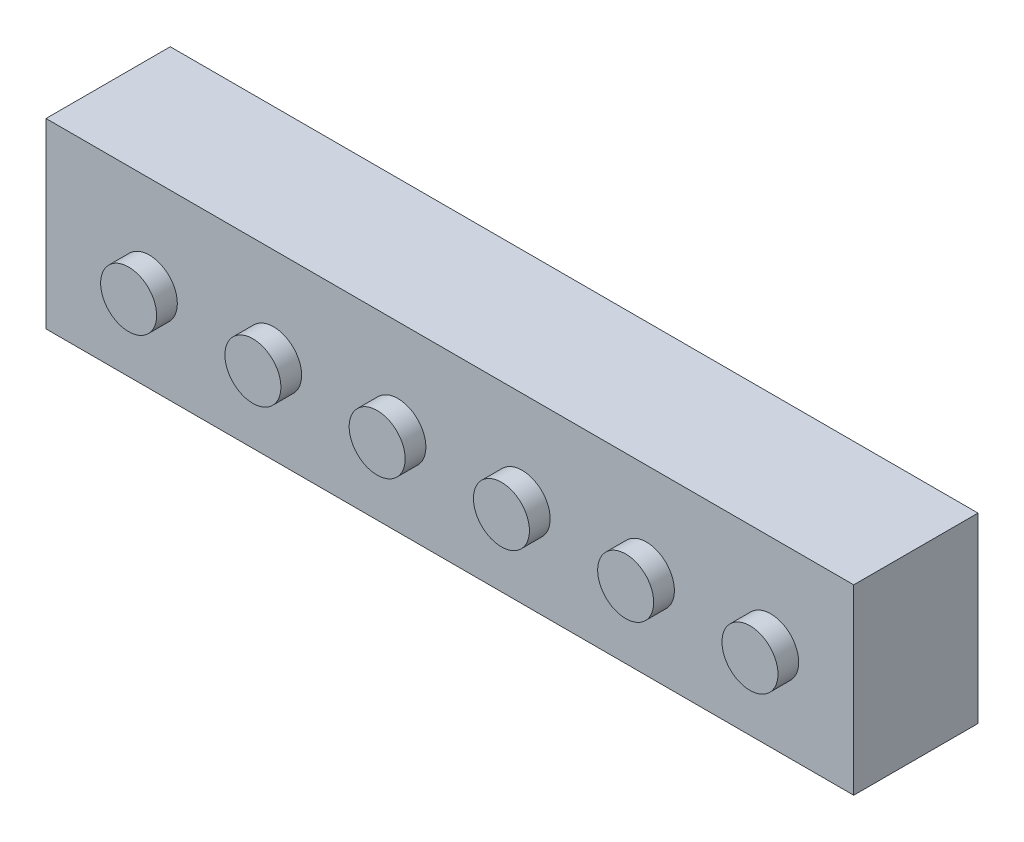
SolidWorks part; units mm, degrees
material "CA"
ref_plane "Front Plane" through (0, 0, 0) normal (0, 0, 1) x (1, 0, 0)
ref_plane "Top Plane" through (0, 0, 0) normal (0, 1, 0) x (1, 0, 0)
ref_plane "Right Plane" through (0, 0, 0) normal (1, 0, 0) x (0, 0, -1)
sketch "Sketch1" plane through (0, 0, 0) normal (0, 0, 1) x (1, 0, 0)
  line L1 (-192.465, 63.375) -> (197.535, 63.375)
  line L2 (-192.465, 63.375) -> (-192.465, -24.625)
  line L3 (-192.465, -24.625) -> (197.535, -24.625)
  line L4 (197.535, 63.375) -> (197.535, -24.625)
  dimension "D1" = 390
  dimension "D2" = 88
extrude "Boss-Extrude1" add sketch "Sketch1" along normal blind 60
sketch "Sketch2" plane through (0, 0, 60) normal (0, 0, 1) x (1, 0, 0)
  circle A0 centre (-142.5695, 17.705) radius 13.5201
extrude "Boss-Extrude2" add sketch "Sketch2" along normal blind 10
pattern_linear "LPattern1" count 6 spacing 60 along (1, 0, 0) of "Boss-Extrude2"
